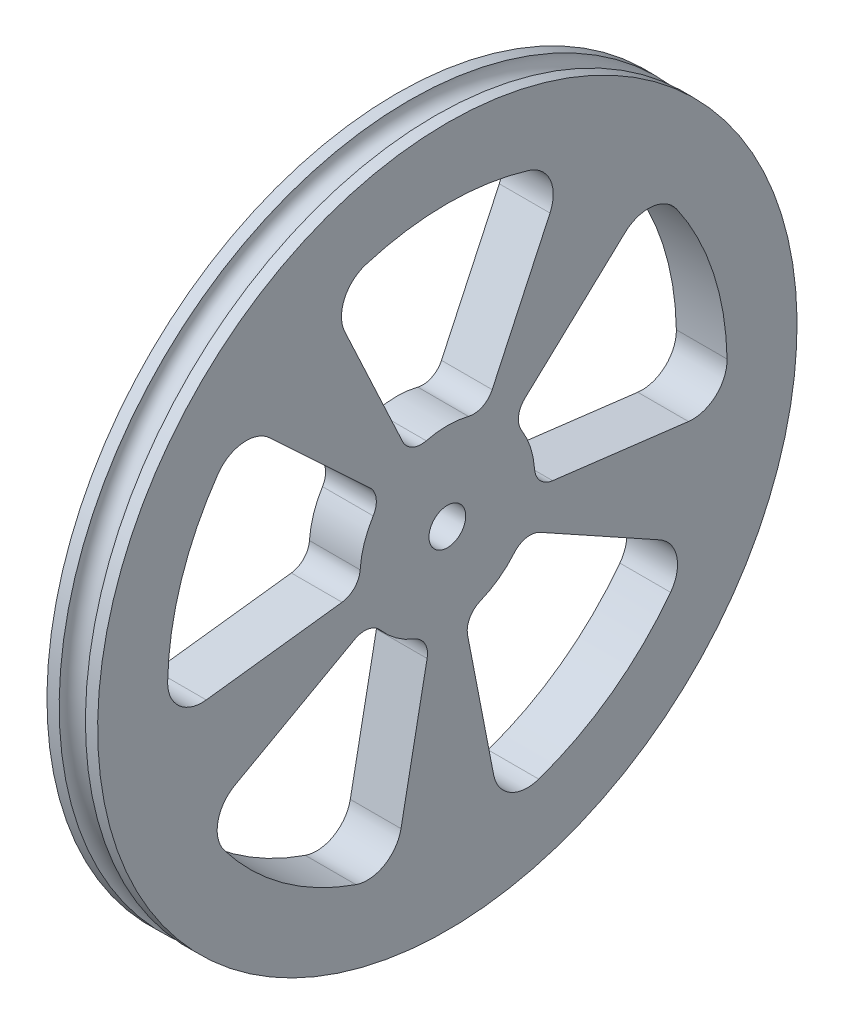
SolidWorks part; units mm, degrees
ref_plane "Front Plane" through (0, 0, 0) normal (0, 0, 1) x (1, 0, 0)
ref_plane "Top Plane" through (0, 0, 0) normal (0, 1, 0) x (1, 0, 0)
ref_plane "Right Plane" through (0, 0, 0) normal (1, 0, 0) x (0, 0, -1)
sketch "Sketch1" plane through (0, 0, 0) normal (0, 0, 1) x (1, 0, 0)
  line L0 (1.905, 50.8) -> (3.683, 50.8)
  line L1 (3.683, 50.8) -> (3.683, 0)
  line L2 (3.683, 0) -> (-3.683, 0)
  line L3 (-3.683, 0) -> (-3.683, 50.8)
  line L4 (-3.683, 50.8) -> (-1.905, 50.8)
  arc A0 (-1.905, 50.8) -> (1.905, 50.8) centre (0, 50.8) ccw
  dimension "D1" = 3.81
  dimension "D2" = 50.8
  dimension "D3" = 1.778
  dimension "D4" = 1.778
  dimension "D5" = 50.8
revolve "Revolve1" add sketch "Sketch1" angle 360 about L2
sketch "Sketch2" plane through (3.683, 0, 0) normal (1, 0, 0) x (0, 0, -1)
  line L0 (0, 38.1) -> (0, 12.7) construction
  line L1 (-38.1, 0) -> (44.4824, 0) construction
  line L2 (-5.3673, 11.5101) -> (-17.1752, 36.8323)
  line L3 (5.3673, 11.5101) -> (17.1752, 36.8323)
  line L4 (0, -12.7) -> (0, -43.7112) construction
  line L5 (9.2882, 8.6614) -> (29.7222, 27.7164)
  line L6 (12.6053, -1.5477) -> (40.3371, -4.9528)
  line L7 (36.2353, 11.7735) -> (12.0784, 3.9245) construction
  line L8 (11.1077, -6.1571) -> (35.5445, -19.7027)
  line L9 (2.4233, -12.4667) -> (7.7545, -39.8933)
  line L10 (22.3946, -30.8235) -> (7.4649, -10.2745) construction
  line L11 (-2.4233, -12.4667) -> (-7.7545, -39.8933)
  line L12 (-11.1077, -6.1571) -> (-35.5445, -19.7027)
  line L13 (-22.3946, -30.8235) -> (-7.4649, -10.2745) construction
  line L14 (-12.6053, -1.5477) -> (-40.3371, -4.9528)
  line L15 (-9.2882, 8.6614) -> (-29.7222, 27.7164)
  line L16 (-36.2353, 11.7735) -> (-12.0784, 3.9245) construction
  line L17 (0, 0) -> (5.3673, 11.5101) construction
  arc A0 (12.6053, -1.5477) -> (9.2882, 8.6614) centre (0, 0) ccw
  arc A1 (40.3371, -4.9528) -> (29.7222, 27.7164) centre (0, 0) ccw
  arc A2 (5.3673, 11.5101) -> (-5.3673, 11.5101) centre (0, 0) ccw
  arc A3 (17.1752, 36.8323) -> (-17.1752, 36.8323) centre (0, 0) ccw
  arc A4 (2.4233, -12.4667) -> (11.1077, -6.1571) centre (0, 0) ccw
  arc A5 (7.7545, -39.8933) -> (35.5445, -19.7027) centre (0, 0) ccw
  arc A6 (-11.1077, -6.1571) -> (-2.4233, -12.4667) centre (0, 0) ccw
  arc A7 (-35.5445, -19.7027) -> (-7.7545, -39.8933) centre (0, 0) ccw
  arc A8 (-9.2882, 8.6614) -> (-12.6053, -1.5477) centre (0, 0) ccw
  arc A9 (-29.7222, 27.7164) -> (-40.3371, -4.9528) centre (0, 0) ccw
  dimension "D1" = 5
  dimension "D2" = 12.7
  dimension "D3" = 25
  dimension "D4" = 38.1
  dimension "D5" = 40.64
extrude "Cut-Extrude1" cut sketch "Sketch2" against normal through all
fillet "Fillet1" radius 5 1 edges at (0, -39.8933, -7.7545)
fillet "Fillet2" radius 5 1 edges at (0, -19.7027, -35.5445)
fillet "Fillet3" radius 5 1 edges at (0, 27.7164, -29.7222)
fillet "Fillet4" radius 5 1 edges at (0, -4.9528, -40.3371)
fillet "Fillet5" radius 5 1 edges at (0, 36.8323, -17.1752)
fillet "Fillet6" radius 5 1 edges at (0, 36.8323, 17.1752)
fillet "Fillet7" radius 5 1 edges at (0, -4.9528, 40.3371)
fillet "Fillet8" radius 5 1 edges at (0, 27.7164, 29.7222)
fillet "Fillet9" radius 5 1 edges at (0, -19.7027, 35.5445)
fillet "Fillet10" radius 5 1 edges at (0, -39.8933, 7.7545)
fillet "Fillet11" radius 3 1 edges at (0, 11.5101, 5.3673)
fillet "Fillet12" radius 3 1 edges at (0, 11.5101, -5.3673)
fillet "Fillet13" radius 3 1 edges at (0, -1.5477, 12.6053)
fillet "Fillet14" radius 3 1 edges at (0, 8.6614, 9.2882)
fillet "Fillet15" radius 3 1 edges at (0, -6.1571, 11.1077)
fillet "Fillet16" radius 3 1 edges at (0, -12.4667, 2.4233)
fillet "Fillet17" radius 3 1 edges at (0, -12.4667, -2.4233)
fillet "Fillet18" radius 3 1 edges at (0, -6.1571, -11.1077)
fillet "Fillet19" radius 3 1 edges at (0, -1.5477, -12.6053)
fillet "Fillet20" radius 3 1 edges at (0, 8.6614, -9.2882)
sketch "Sketch4" plane through (-3.683, 0, 0) normal (-1, 0, 0) x (0, 0, 1)
  circle A0 centre (0, 0) radius 2.667
  dimension "D1" = 5.334
extrude "Cut-Extrude2" cut sketch "Sketch4" against normal through all
